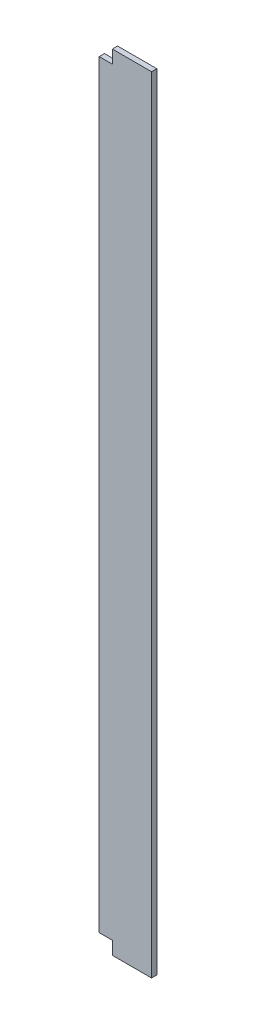
SolidWorks part; units mm, degrees
ref_plane "Plano frontal" through (0, 0, 0) normal (0, 0, 1) x (1, 0, 0)
ref_plane "Plano superior" through (0, 0, 0) normal (0, 1, 0) x (1, 0, 0)
ref_plane "Plano direito" through (0, 0, 0) normal (1, 0, 0) x (0, 0, -1)
sketch "Esboço1" plane through (0, 0, 0) normal (0, 1, 0) x (1, 0, 0)
  line L5 (-1156.4837, 804.6872) -> (-956.4837, 804.6872)
  line L6 (-1156.4837, 804.6872) -> (-1156.4837, 784.6872)
  line L7 (-1156.4837, 784.6872) -> (-956.4837, 784.6872)
  line L8 (-956.4837, 804.6872) -> (-956.4837, 784.6872)
  dimension "D1" = 200
  dimension "D2" = 20
extrude "Ressalto-extrusão1" add sketch "Esboço1" along normal blind 3000 contours L5 L8 L7 L6
sketch "Esboço2" plane through (0, 0, -784.6872) normal (0, 0, 1) x (1, 0, 0)
  line L1 (-1106.4837, 0) -> (-1156.4837, 0)
  line L2 (-1106.4837, 0) -> (-1106.4837, 50)
  line L3 (-1106.4837, 50) -> (-1156.4837, 50)
  line L4 (-1156.4837, 0) -> (-1156.4837, 50)
  line L5 (-1156.4837, 3000) -> (-1156.4837, 0) construction
  dimension "D1" = 50
  dimension "D2" = 50
extrude "Corte-extrusão1" cut sketch "Esboço2" against normal through all
sketch "Esboço3" plane through (0, 0, -784.6872) normal (0, 0, 1) x (1, 0, 0)
  line L0 (-1156.4837, 3000) -> (-1156.4837, 50) construction
  line L1 (-1106.4837, 3000) -> (-1156.4837, 3000)
  line L2 (-1106.4837, 3000) -> (-1106.4837, 2950)
  line L3 (-1106.4837, 2950) -> (-1156.4837, 2950)
  line L4 (-1156.4837, 3000) -> (-1156.4837, 2950)
  dimension "D1" = 50
  dimension "D2" = 50
extrude "Corte-extrusão2" cut sketch "Esboço3" against normal through all
